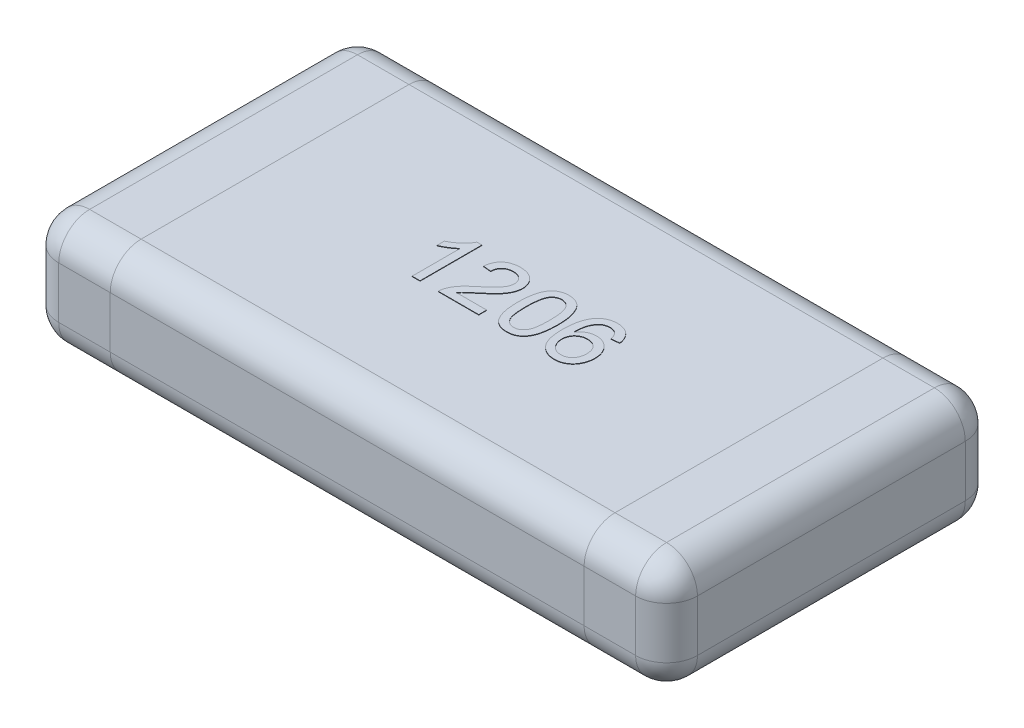
SolidWorks part; units mm, degrees
ref_plane "Front" through (0, 0, 0) normal (0, 0, 1) x (1, 0, 0)
ref_plane "Top" through (0, 0, 0) normal (0, 1, 0) x (1, 0, 0)
ref_plane "Right" through (0, 0, 0) normal (1, 0, 0) x (0, 0, -1)
sketch "Sketch1" plane through (0, 0, 0) normal (0, 1, 0) x (1, 0, 0)
  line L0 (0, -5.3126) -> (0, 5.729) construction
  line L1 (-6.1479, 0) -> (7.7291, 0) construction
  line L3 (-1.55, 0.8) -> (1.55, 0.8)
  line L4 (-1.55, 0.8) -> (-1.55, -0.8)
  line L5 (-1.55, -0.8) -> (1.55, -0.8)
  line L6 (1.55, 0.8) -> (1.55, -0.8)
  dimension "D1" = 3.1
  dimension "D2" = 1.6
extrude "Extrude1" add sketch "Sketch1" along normal blind 0.55
fillet "Fillet1" radius 0.15 12 edges at (0, 0.55, 0.8) (-1.55, 0.275, -0.8) (0, 0, -0.8) (-1.55, 0, 0) (-1.55, 0.275, 0.8) (0, 0, 0.8) (1.55, 0.275, 0.8) (1.55, 0.275, -0.8) (1.55, 0, 0) (0, 0.55, -0.8) (1.55, 0.55, 0) (-1.55, 0.55, 0)
sketch "Sketch2" plane through (0, 0, 0.8) normal (0, 0, 1) x (1, 0, 0)
  line L0 (-1.4, 0.55) -> (1.4, 0.55) construction
  line L1 (-1.15, 0.55) -> (1.15, 0.55)
  line L2 (-1.15, 0.55) -> (-1.15, 0)
  line L3 (-1.15, 0) -> (1.15, 0)
  line L4 (1.15, 0.55) -> (1.15, 0)
  line L5 (1.4, 0) -> (-1.4, 0) construction
  line L6 (-1.55, 0.15) -> (-1.55, 0.4) construction
  line L7 (0, -0.2963) -> (0, 3.0124) construction
  dimension "D1" = 0.4
split line "Split Line1"
sketch "Sketch3" plane through (0, 0.55, 0) normal (0, 1, 0) x (1, 0, 0)
  text T0 "1206" font "Arial" height 0.3
  dimension "D1" = 0.45
  dimension "D2" = 0.15
extrude "Extrude2" add sketch "Sketch3" along normal blind 0.002
